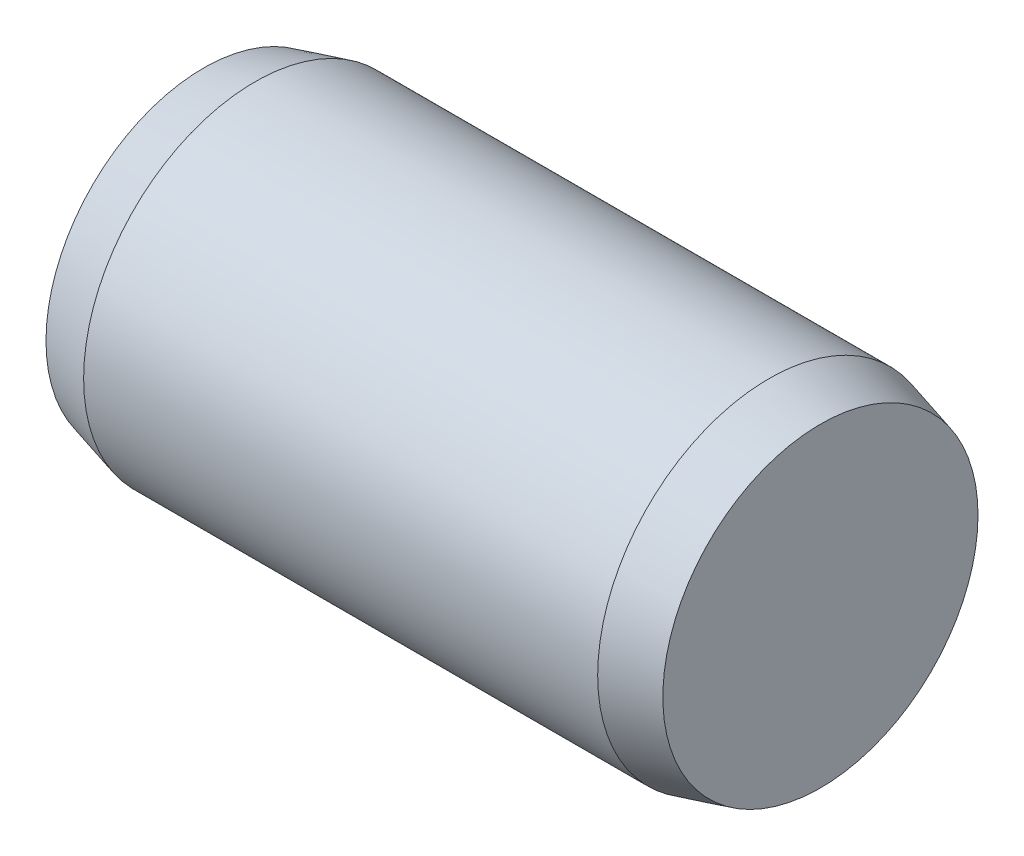
SolidWorks part; units mm, degrees
ref_plane "Front Plane" through (0, 0, 0) normal (0, 0, 1) x (1, 0, 0)
ref_plane "Top Plane" through (0, 0, 0) normal (0, 1, 0) x (1, 0, 0)
ref_plane "Right Plane" through (0, 0, 0) normal (1, 0, 0) x (0, 0, -1)
sketch "Sketch1" plane through (0, 0, 0) normal (0, 0, 1) x (1, 0, 0)
  line L0 (-3, 0) -> (3, 0) construction
  line L1 (3, 2) -> (3, -2) construction
  line L2 (-3, 2) -> (-3, -2) construction
  line L3 (3.6, 2) -> (3.6, -2) construction
  line L4 (-3.6, 2) -> (-3.6, -2) construction
  line L5 (-3, 0) -> (-3.6, 0) construction
  line L6 (3, 0) -> (3.6, 0) construction
  dimension "D1" = 0.6
  dimension "Dia" = 4
  dimension "Length" = 6
  dimension "C" = 0.6
sketch "Sketch2" plane through (0, 0, 0) normal (1, 0, 0) x (0, 0, -1)
  circle A0 centre (0, 0) radius 2
extrude "Extrude1" add sketch "Sketch2" against normal up to vertex (3 mm away) and the other way up to vertex (3 mm away) up to point (-3, 2, 0) other way up to point (3, 2, 0)
sketch "Sketch3" plane through (3, 0, 0) normal (1, 0, 0) x (0, 0, -1)
  circle A1 centre (0, 0) radius 2
  circle A2 centre (0, 0) radius 2
  dimension "D1" = 0
extrude "Extrude2" add sketch "Sketch3" along normal up to vertex (0.6 mm away) draft 15 up to point (3.6, 0, 0)
sketch "Sketch4" plane through (-3, 0, 0) normal (-1, 0, 0) x (0, 0, 1)
  circle A1 centre (0, 0) radius 2
  circle A2 centre (0, 0) radius 2
  dimension "D1" = 0
extrude "Extrude3" add sketch "Sketch4" along normal up to vertex (0.6 mm away) draft 15 up to point (-3.6, 0, 0)
equation "\"D1@Sketch1\" = \"C@Sketch1\""
